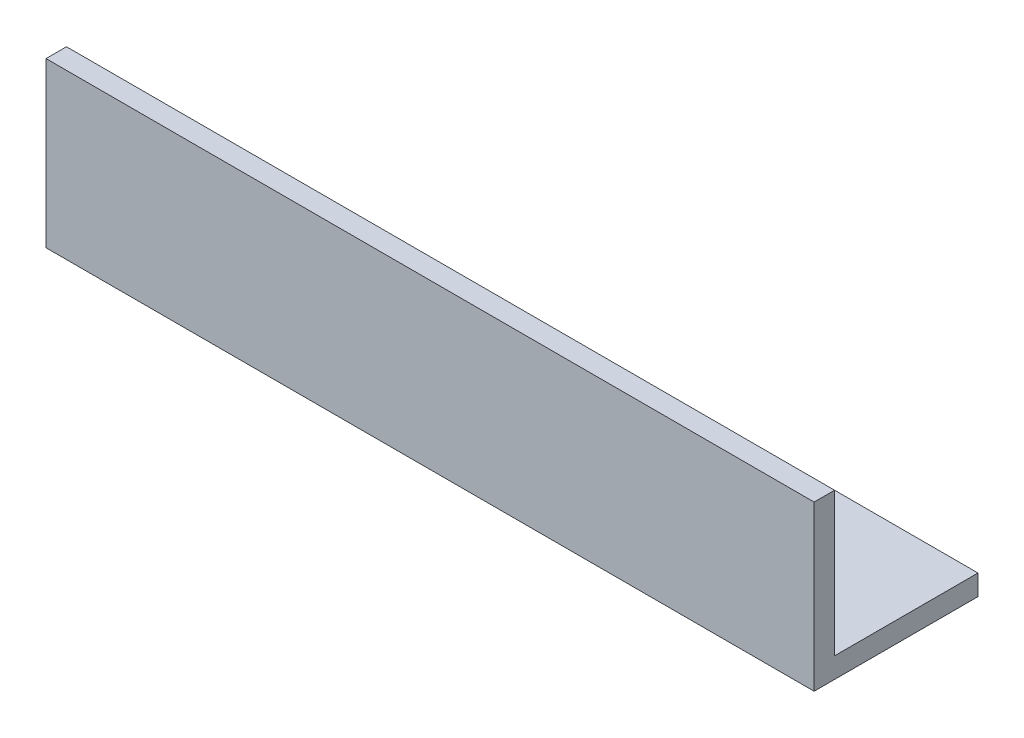
SolidWorks part; units mm, degrees
ref_plane "Спереди" through (0, 0, 0) normal (0, 0, 1) x (1, 0, 0)
ref_plane "Сверху" through (0, 0, 0) normal (0, 1, 0) x (1, 0, 0)
ref_plane "Справа" through (0, 0, 0) normal (1, 0, 0) x (0, 0, -1)
sketch "Эскиз1" plane through (0, 0, 0) normal (1, 0, 0) x (0, 0, -1)
  line L0 (0, 0) -> (0, 32)
  line L1 (0, 0) -> (32, 0)
extrude "Вытянуть-Тонкостенный1" add sketch "Эскиз1" along normal blind 150 thin
sketch "Эскиз2" plane through (0, 0, 0) normal (0, -1, 0) x (1, 0, 0)
  line L0 (75, -34.4537) -> (75, 3.8067) construction
  circle A0 centre (130, -13) radius 5
  circle A1 centre (100, -13) radius 5
  circle A2 centre (50, -13) radius 5
  circle A3 centre (20, -13) radius 5
  dimension "D1" = 2
extrude "Вырез-Вытянуть1" cut sketch "Эскиз2" against normal through all
